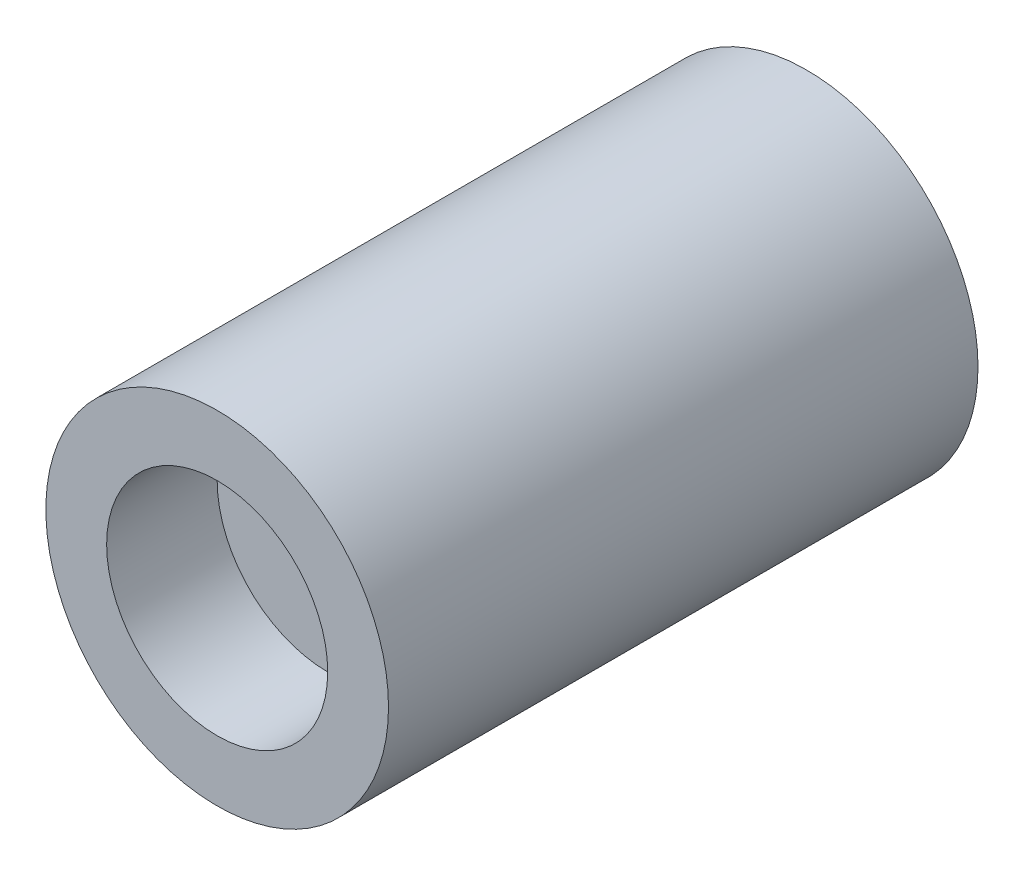
SolidWorks part; units mm, degrees
ref_plane "Front Plane" through (0, 0, 0) normal (0, 0, 1) x (1, 0, 0)
ref_plane "Top Plane" through (0, 0, 0) normal (0, 1, 0) x (1, 0, 0)
ref_plane "Right Plane" through (0, 0, 0) normal (1, 0, 0) x (0, 0, -1)
sketch "Sketch1" plane through (0, 0, 0) normal (0, 0, 1) x (1, 0, 0)
  circle A0 centre (0, 0) radius 23.25
  dimension "D1" = 46.5
extrude "Boss-Extrude1" add sketch "Sketch1" along normal blind 80
sketch "Sketch2" plane through (0, 0, 80) normal (0, 0, 1) x (1, 0, 0)
  circle A0 centre (0, 0) radius 15
  dimension "D1" = 30
extrude "Cut-Extrude4" cut sketch "Sketch2" against normal blind 15 contours A0
